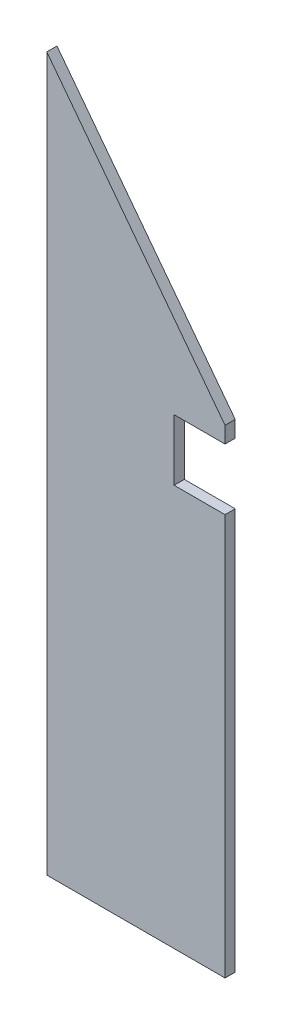
SolidWorks part; units mm, degrees
ref_plane "Front" through (0, 0, 0) normal (0, 0, 1) x (1, 0, 0)
ref_plane "Top" through (0, 0, 0) normal (0, 1, 0) x (1, 0, 0)
ref_plane "Right" through (0, 0, 0) normal (1, 0, 0) x (0, 0, -1)
sketch "Sketch1" plane through (0, 0, 0) normal (0, 0, 1) x (1, 0, 0)
  line L0 (0, 350) -> (87.5, 235)
  line L1 (0, 0) -> (87.5, 0)
  line L2 (0, 0) -> (0, 350)
  line L4 (87.5, 0) -> (87.5, 197)
  line L5 (87.5, 197) -> (62.5, 197)
  line L6 (62.5, 197) -> (62.5, 227)
  line L7 (62.5, 227) -> (87.5, 227)
  line L8 (87.5, 227) -> (87.5, 235)
  dimension "D1" = 87.5
  dimension "D2" = 350
  dimension "D3" = 115
  dimension "D4" = 30
  dimension "D5" = 25
  dimension "D6" = 8
extrude "Boss-Extrude1" add sketch "Sketch1" along normal blind 5
